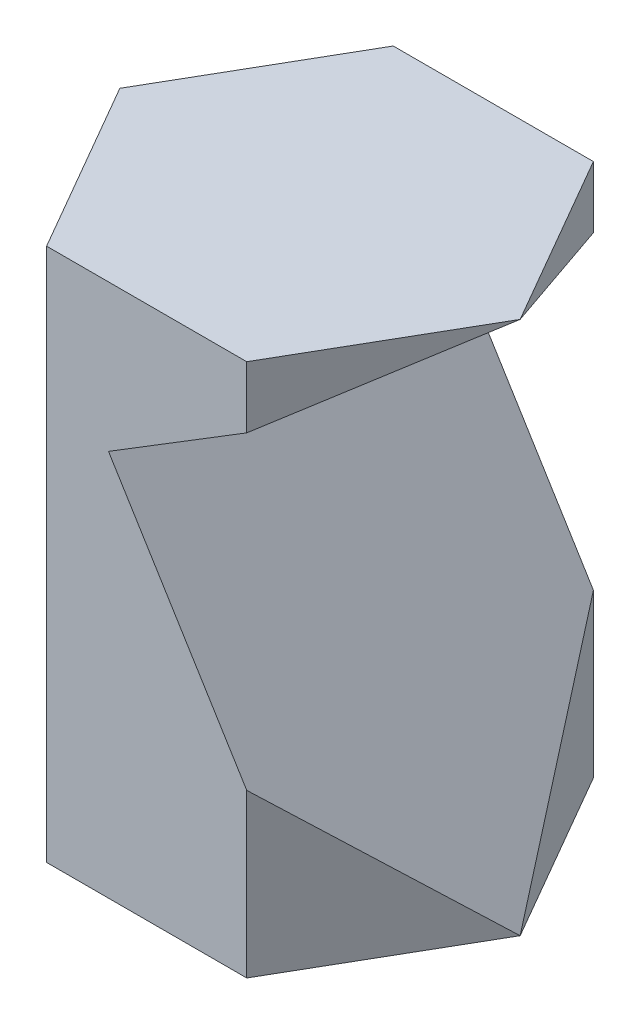
SolidWorks part; units mm, degrees
ref_plane "Front Plane" through (0, 0, 0) normal (0, 0, 1) x (1, 0, 0)
ref_plane "Top Plane" through (0, 0, 0) normal (0, 1, 0) x (1, 0, 0)
ref_plane "Right Plane" through (0, 0, 0) normal (1, 0, 0) x (0, 0, -1)
sketch "Sketch1" plane through (0, 0, 0) normal (0, 1, 0) x (1, 0, 0)
  line L1 (45, -61.9615) -> (60, -35.9808)
  line L2 (60, -35.9808) -> (45, -10)
  line L3 (45, -10) -> (15, -10)
  line L4 (15, -10) -> (0, -35.9808)
  line L5 (0, -35.9808) -> (15, -61.9615)
  line L6 (15, -61.9615) -> (45, -61.9615)
  circle A0 centre (30, -35.9808) radius 25.9808 construction
  dimension "D1" = 30
  dimension "D2" = 10
extrude "Boss-Extrude1" add sketch "Sketch1" along normal blind 80
sketch "Sketch2" plane through (0, 0, 0) normal (0, 0, 1) x (1, 0, 0)
  line L0 (60, 80) -> (24.2789, 58)
  line L1 (60, 80) -> (95.7211, 22)
  line L2 (24.2789, 58) -> (60, 0)
  line L3 (95.7211, 22) -> (60, 0)
  dimension "D1" = 22
extrude "Cut-Extrude2" cut sketch "Sketch2" along normal through all
